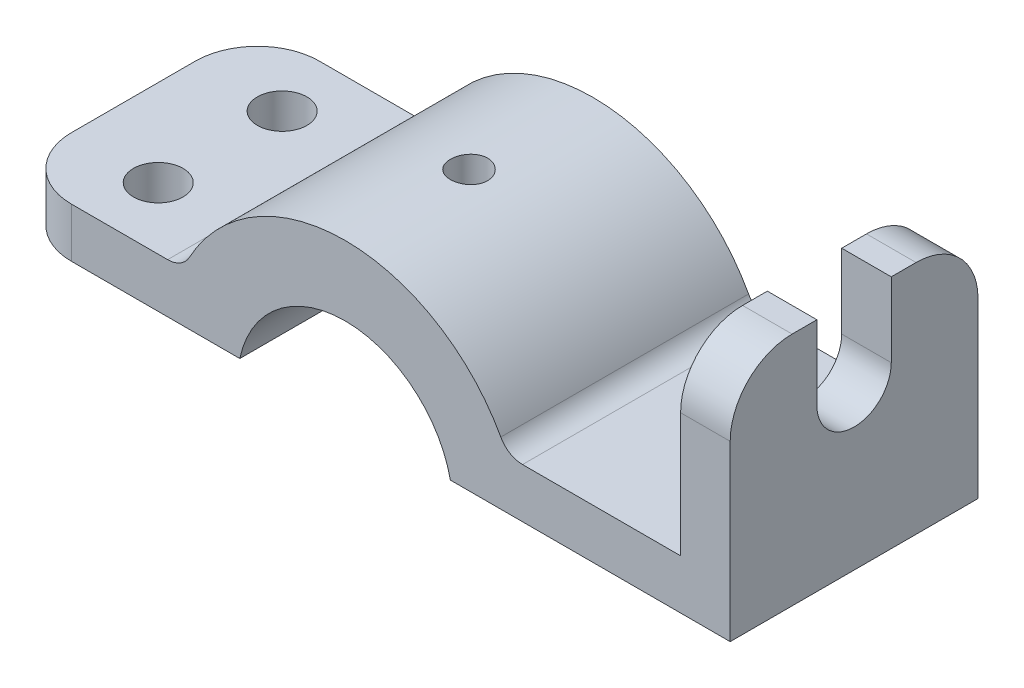
SolidWorks part; units mm, degrees
ref_plane "Piano frontale" through (0, 0, 0) normal (0, 0, 1) x (1, 0, 0)
ref_plane "Piano superiore" through (0, 0, 0) normal (0, 1, 0) x (1, 0, 0)
ref_plane "Piano destro" through (0, 0, 0) normal (1, 0, 0) x (0, 0, -1)
sketch "Schizzo2" plane through (0, 0, 0) normal (0, 0, 1) x (1, 0, 0)
  line L0 (-27.0793, 0) -> (-27.0793, 4)
  line L1 (55, 0) -> (-55, 0) construction
  line L2 (-27.0793, 4) -> (-13.0793, 4)
  line L3 (13.0793, 4) -> (27.0793, 4)
  line L4 (-27.0793, 0) -> (-8.4968, 0)
  line L5 (8.4968, 0) -> (31.0793, 0)
  line L6 (27.0793, 4) -> (27.0793, 19)
  line L7 (27.0793, 19) -> (31.0793, 19)
  line L8 (31.0793, 19) -> (31.0793, 0)
  line L13 (0, -55) -> (0, 55) construction
  arc A0 (-13.0793, 4) -> (13.0793, 4) centre (0, -1.8023) cw
  arc A2 (-8.4968, 0) -> (8.4968, 0) centre (0, -1.8023) cw
  point P15 (0, 0)
  dimension "D6" = 8.6859
  dimension "D7" = 14.3086
  dimension "D1" = 4
  dimension "D2" = 4
  dimension "D3" = 58.1586
  dimension "D4" = 14
  dimension "D5" = 14
  dimension "D9" = 15
extrude "Estrusione-Estrusione1" add sketch "Schizzo2" along normal mid plane 20
fillet "Raccordo1" radius 5 2 edges at (29.0793, 19, -10) (29.0793, 19, 10)
fillet "Raccordo2" radius 5 2 edges at (-27.0793, 2, -10) (-27.0793, 2, 10)
fillet "Raccordo3" radius 2 2 edges at (-13.0793, 4, 0) (13.0793, 4, 0)
sketch "Schizzo3" plane through (0, 4, 0) normal (0, 1, 0) x (1, 0, 0)
  line L0 (-16.934, 0) -> (16.934, 0) construction
  line L2 (-27.0793, -5) -> (-27.0793, 5) construction
  circle A0 centre (-20.0793, 5) radius 2
  dimension "D1" = 4
  dimension "D2" = 5
  dimension "D3" = 7
extrude "Taglio-Estrusione1" cut sketch "Schizzo3" against normal blind 20
mirror "Specchia1" about plane through (0, 0, 0) normal (0, 0, 1) of "Taglio-Estrusione1"
sketch "Schizzo5" plane through (0, 0, 0) normal (0, 1, 0) x (1, 0, 0)
  circle A0 centre (0, 0) radius 1.5
  dimension "D1" = 3
extrude "Taglio-Estrusione2" cut sketch "Schizzo5" along normal blind 20
sketch "Schizzo7" plane through (31.0793, 0, 0) normal (1, 0, 0) x (0, 0, -1)
  line L0 (-3, 19) -> (-3, 13)
  line L1 (-5, 19) -> (5, 19) construction
  line L2 (3, 19) -> (3, 13)
  line L3 (-3, 19) -> (3, 19)
  line L4 (0, 16.934) -> (0, -16.934) construction
  arc A0 (-3, 13) -> (3, 13) centre (0, 13) ccw
  point P7 (0, 0)
  dimension "D3" = 6
  dimension "D1" = 3
  dimension "D2" = 3
extrude "Taglio-Estrusione3" cut sketch "Schizzo7" against normal blind 20
